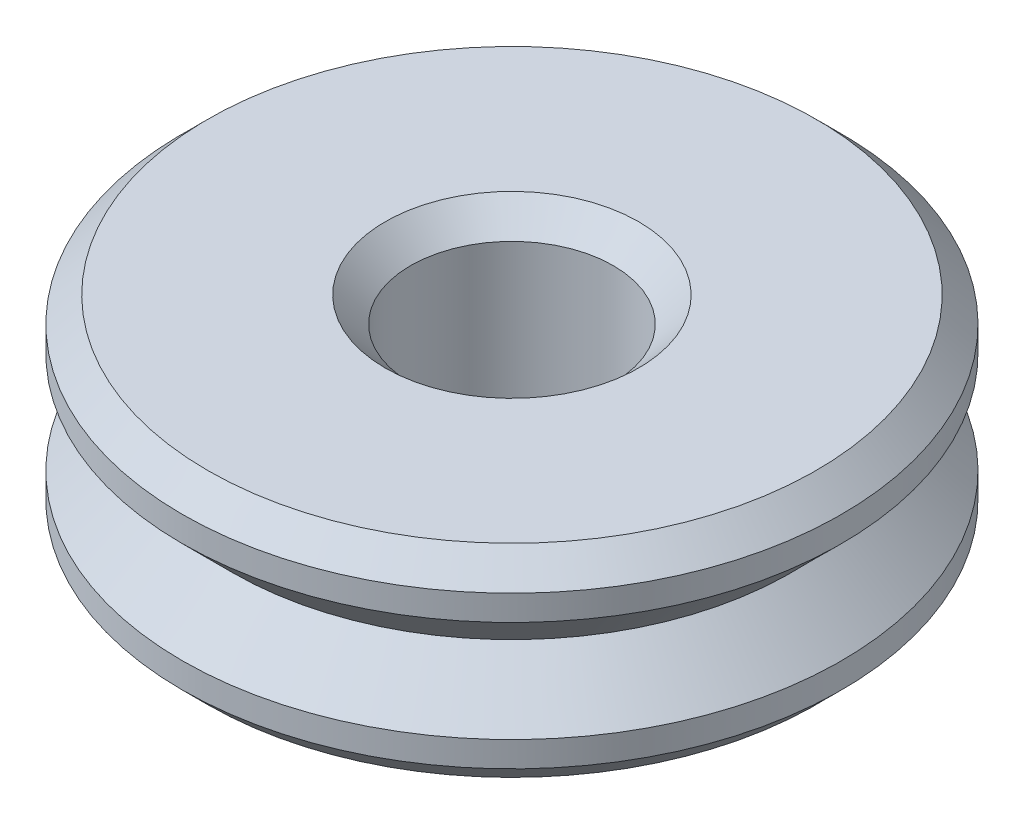
SolidWorks part; units mm, degrees
ref_plane "Front" through (0, 0, 0) normal (0, 0, 1) x (1, 0, 0)
ref_plane "Top" through (0, 0, 0) normal (0, 1, 0) x (1, 0, 0)
ref_plane "Right" through (0, 0, 0) normal (1, 0, 0) x (0, 0, -1)
sketch "Sketch1" plane through (0, 0, 0) normal (0, 1, 0) x (1, 0, 0)
  circle A0 centre (0, 0) radius 6.5
  circle A1 centre (0, 0) radius 2
  dimension "D1" = 13
  dimension "D2" = 4
extrude "Boss-Extrude1" add sketch "Sketch1" along normal blind 4
ref_plane "Plane1" through (0, 2, 0) normal (0, 1, 0) x (1, 0, 0)
sketch "Sketch2" plane through (0, 0, 0) normal (1, 0, 0) x (0, 0, -1)
  line L0 (-6.5, 3) -> (-6.5, 1)
  line L1 (-6.5, 4) -> (-6.5, 0) construction
  line L2 (-6.5, 4) -> (-6.5, 0) construction
  line L3 (-6.5, 1) -> (-5.5, 2)
  line L4 (50, 2) -> (-50, 2) construction
  line L5 (-5.5, 2) -> (-6.5, 3)
  dimension "D1" = 1
  dimension "D2" = 1
  dimension "D3" = 1
revolve "Cut-Revolve1" cut sketch "Sketch2" angle 360 about axis through (0, 4, 0) along (0, -1, 0)
chamfer "Chamfer1" distance 0.5 angle 45 4 edges at (0, 0, 2) (0, 0, 6.5) (0, 4, 6.5) (0, 4, 2)
